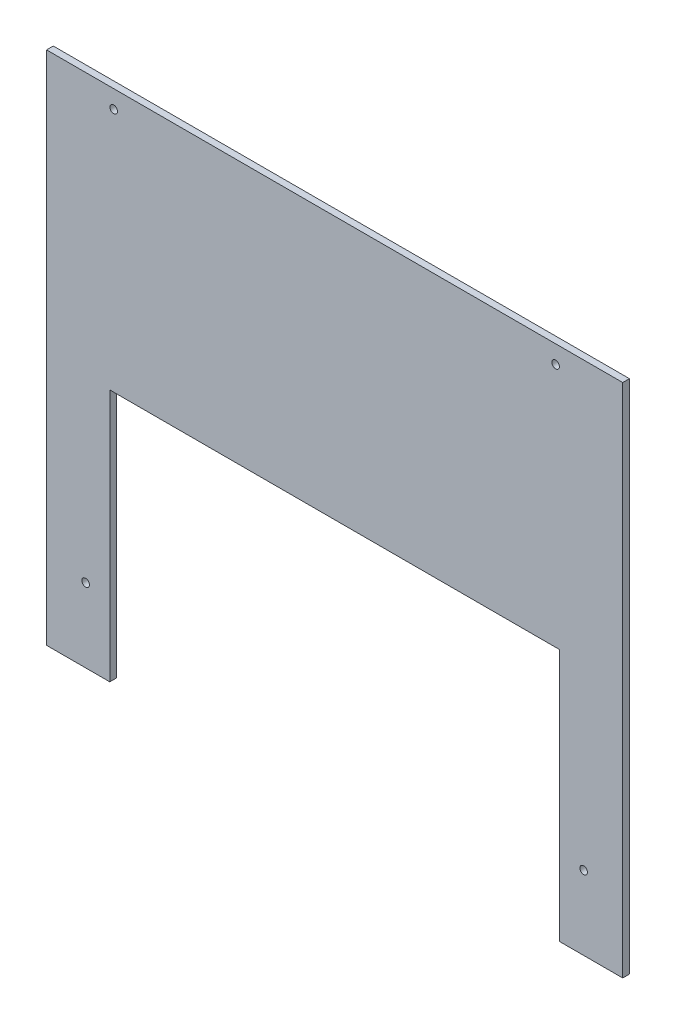
SolidWorks part; units mm, degrees
ref_plane "Plan de face" through (0, 0, 0) normal (0, 0, 1) x (1, 0, 0)
ref_plane "Plan de dessus" through (0, 0, 0) normal (0, 1, 0) x (1, 0, 0)
ref_plane "Plan de droite" through (0, 0, 0) normal (1, 0, 0) x (0, 0, -1)
sketch "Esquisse2" plane through (0, 0, 0) normal (0, 0, 1) x (1, 0, 0)
  line L0 (229.255, -230.48) -> (257.51, -230.48)
  line L1 (0, 0) -> (257.51, 0)
  line L2 (0, 0) -> (0, -230.48)
  line L3 (0, -230.48) -> (28.255, -230.48)
  line L4 (257.51, 0) -> (257.51, -230.48)
  line L6 (28.255, -230.48) -> (28.255, -117.48)
  line L7 (28.255, -117.48) -> (229.255, -117.48)
  line L8 (229.255, -230.48) -> (229.255, -117.48)
  line L9 (30, -8) -> (227.51, -8) construction
  line L10 (17.455, -197.48) -> (240.055, -197.48) construction
  line L11 (128.755, 0) -> (128.755, -197.48) construction
  circle A0 centre (17.455, -197.48) radius 1.7
  circle A1 centre (240.055, -197.48) radius 1.7
  circle A2 centre (227.51, -8) radius 1.7
  circle A3 centre (30, -8) radius 1.7
  point P19 (128.755, -8)
  dimension "D1" = 222.6
  dimension "D3" = 3.4
  dimension "D2" = 197.51
  dimension "D4" = 201
  dimension "D5" = 8
  dimension "D6" = 33
  dimension "D7" = 257.51
  dimension "D8" = 230.48
  dimension "D9" = 113
extrude "Boss.-Extru.1" add sketch "Esquisse2" along normal blind 3
